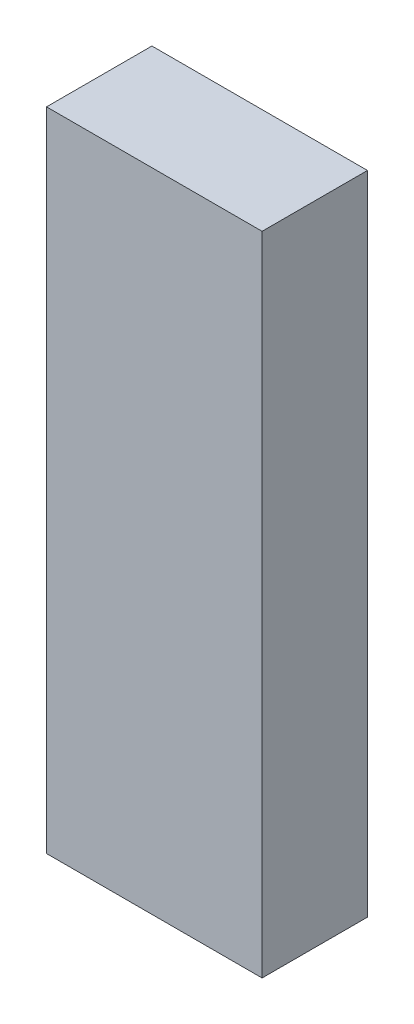
SolidWorks part; units mm, degrees
ref_plane "Front" through (0, 0, 0) normal (0, 0, 1) x (1, 0, 0)
ref_plane "Top" through (0, 0, 0) normal (0, 1, 0) x (1, 0, 0)
ref_plane "Right" through (0, 0, 0) normal (1, 0, 0) x (0, 0, -1)
sketch "Sketch1" plane through (0, 0, 0) normal (0, 1, 0) x (1, 0, 0)
  line L1 (-22.5, -11) -> (22.5, -11)
  line L2 (-22.5, -11) -> (-22.5, 11)
  line L3 (-22.5, 11) -> (22.5, 11)
  line L4 (22.5, -11) -> (22.5, 11)
  line L5 (-22.5, -11) -> (22.5, 11) construction
  line L6 (-22.5, 11) -> (22.5, -11) construction
  point P0 (0, 0)
  dimension "D1" = 45
  dimension "D2" = 22
extrude "Boss-Extrude1" add sketch "Sketch1" along normal mid plane 135
